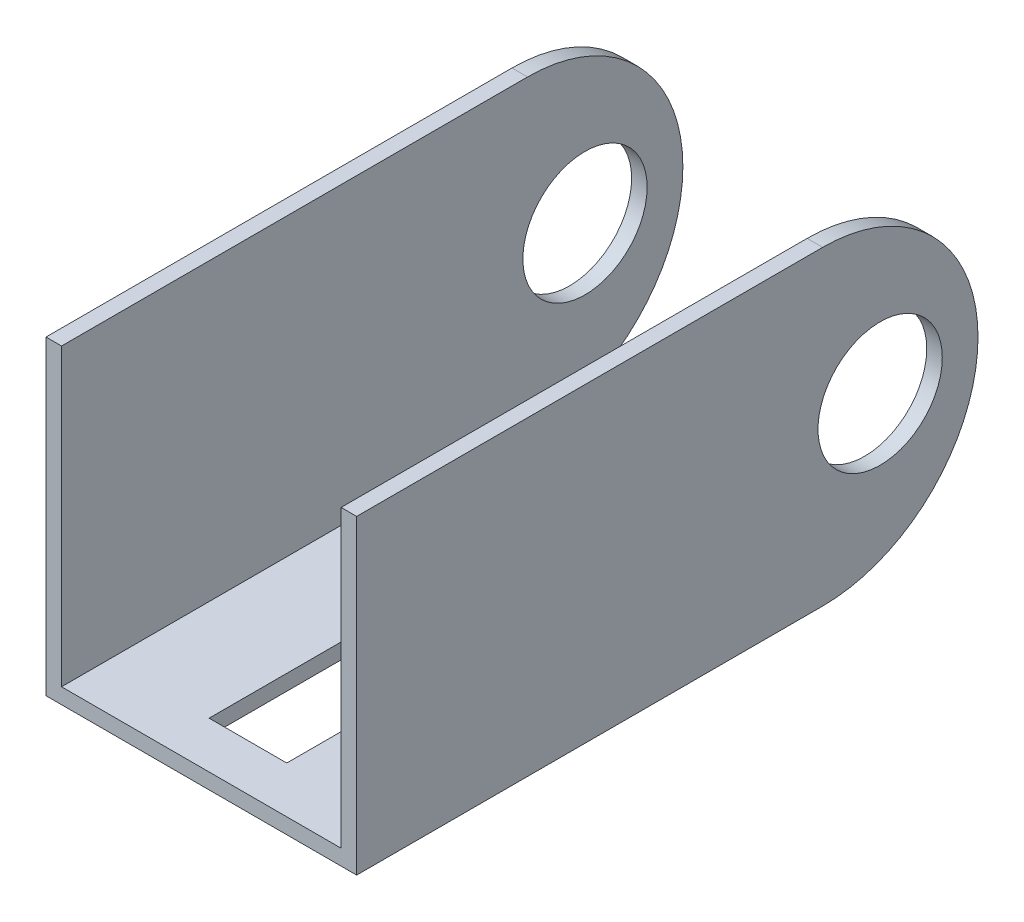
SolidWorks part; units mm, degrees
ref_plane "Alzado" through (0, 0, 0) normal (0, 0, 1) x (1, 0, 0)
ref_plane "Planta" through (0, 0, 0) normal (0, 1, 0) x (1, 0, 0)
ref_plane "Vista lateral" through (0, 0, 0) normal (1, 0, 0) x (0, 0, -1)
sketch "Croquis1" plane through (0, 0, 0) normal (0, 0, 1) x (1, 0, 0)
  line L0 (0, 0) -> (-20, 0)
  line L1 (-20, 0) -> (-20, 20)
  line L2 (-20, 20) -> (-19, 20)
  line L3 (-19, 20) -> (-19, 1)
  line L4 (-19, 1) -> (-1, 1)
  line L5 (-1, 1) -> (-1, 20)
  line L6 (-1, 20) -> (0, 20)
  line L7 (0, 20) -> (0, 0)
  dimension "D1" = 20
  dimension "D2" = 20
  dimension "D3" = 20
  dimension "D4" = 1
  dimension "D5" = 1
  dimension "D6" = 1
extrude "Saliente-Extruir1" add sketch "Croquis1" against normal blind 40
sketch "Croquis2" plane through (0, 0, 0) normal (1, 0, 0) x (0, 0, -1)
  line L0 (40, 10) -> (30, 10) construction
  line L1 (40, 0) -> (40, 20) construction
  line L2 (40, 10) -> (40, 0)
  line L3 (40, 0) -> (30, 0)
  line L4 (40, 10) -> (40, 20)
  line L5 (40, 20) -> (30, 20)
  arc A0 (30, 0) -> (30, 20) centre (30, 10) ccw
  line M4 (0, 0) -> (40, 0)
  line M5 (40, 0) -> (40, 20)
  line M6 (40, 20) -> (0, 20)
  dimension "D1" = 10
extrude "Cortar-Extruir1" cut sketch "Croquis2" against normal blind 40 contours A0 M5 M6 | A0 M4 M5
sketch "Croquis3" plane through (0, 0, 0) normal (1, 0, 0) x (0, 0, -1)
  line L0 (40, 10) -> (33.7, 10) construction
  arc A0 (30, 0) -> (30, 20) centre (30, 10) ccw construction
  circle A1 centre (33.7, 10) radius 4
  dimension "D1" = 6.3
extrude "Cortar-Extruir2" cut sketch "Croquis3" against normal blind 40
ref_plane "Plano1" through (0, 0, 0) normal (0, -1, 0) x (-1, 0, 0)
sketch "Croquis4" plane through (0, 0, 0) normal (0, -1, 0) x (-1, 0, 0)
  line L0 (10, 0) -> (10, 26) construction
  line L1 (20, 0) -> (0, 0) construction
  line L2 (19, 26) -> (1, 26)
  line L4 (19, 26) -> (19, 34.3589)
  line L5 (19, 34.3589) -> (9.8322, 34.3589)
  line L6 (1, 34.3589) -> (1, 26)
  line L7 (1, 34.3589) -> (9.8322, 34.3589)
  point P9 (10, 26)
  dimension "D1" = 26
extrude "Cortar-Extruir3" cut sketch "Croquis4" against normal blind 40
sketch "Croquis5" plane through (0, 0, 0) normal (0, -1, 0) x (1, 0, 0)
  line L0 (-20, 0) -> (0, 0) construction
  line L1 (-7.5, -22) -> (-12.5, -22)
  line L2 (-7.5, -22) -> (-7.5, -3)
  line L3 (-7.5, -3) -> (-12.5, -3)
  line L4 (-12.5, -22) -> (-12.5, -3)
  line L5 (0, -30) -> (0, 0) construction
  dimension "D1" = 19
  dimension "D2" = 5
  dimension "D3" = 3
  dimension "D4" = 7.5
extrude "Cortar-Extruir4" cut sketch "Croquis5" against normal blind 40
